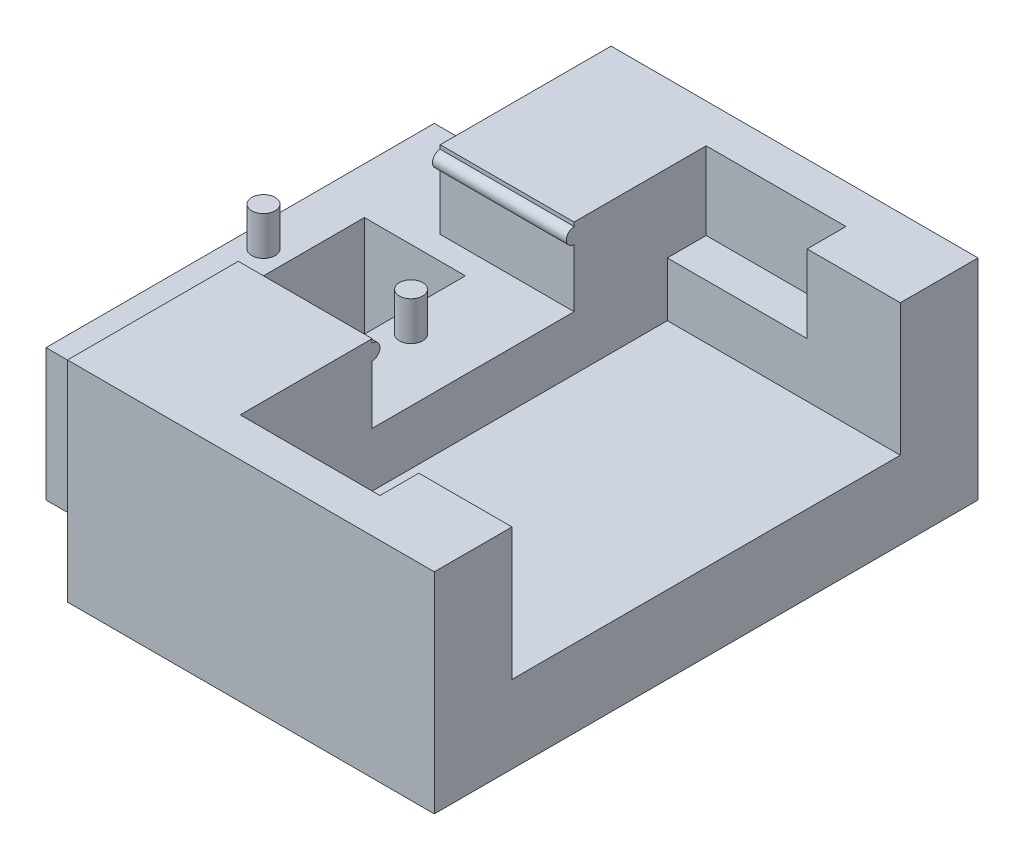
SolidWorks part; units mm, degrees
ref_plane "Front Plane" through (0, 0, 0) normal (0, 0, 1) x (1, 0, 0)
ref_plane "Top Plane" through (0, 0, 0) normal (0, 1, 0) x (1, 0, 0)
ref_plane "Right Plane" through (0, 0, 0) normal (1, 0, 0) x (0, 0, -1)
sketch "Sketch1" plane through (0, 0, 0) normal (0, 1, 0) x (1, 0, 0)
  line L1 (0, 0) -> (15.24, 0)
  line L2 (0, 0) -> (0, 12.7)
  line L3 (0, 12.7) -> (15.24, 12.7)
  line L4 (15.24, 0) -> (15.24, 12.7)
extrude "Main Base" add sketch "Sketch1" along normal blind 2.54
sketch "Sketch2" plane through (0, 2.54, 0) normal (0, 1, 0) x (-1, 0, 0)
  line L0 (0, -6.35) -> (-15.24, -6.35) construction
  line L1 (0, -12.7) -> (0, 0) construction
  line L2 (-15.24, 0) -> (-15.24, -12.7) construction
  circle A0 centre (-0.762, -6.35) radius 0.381
  circle A1 centre (-5.588, -6.35) radius 0.381
extrude "AlignmentPins" add sketch "Sketch2" along normal blind 1.27 from offset 1.778
sketch "Sketch7" plane through (0, 2.54, 0) normal (0, 1, 0) x (1, 0, 0)
  line L0 (0, 0) -> (15.24, 0) construction
  line L1 (0, 12.7) -> (7.62, 12.7)
  line L2 (0, 12.7) -> (0, 0)
  line L3 (0, 0) -> (7.62, 0)
  line L4 (7.62, 12.7) -> (7.62, 0)
extrude "PCBoardEdges" add sketch "Sketch7" along normal blind 1.778
sketch "Sketch12" plane through (0, 4.318, 0) normal (0, 1, 0) x (1, 0, 0)
  line L1 (7.62, 0) -> (3.241, 0)
  line L2 (7.62, 0) -> (7.62, 3.048)
  line L3 (7.62, 3.048) -> (3.241, 3.048)
  line L4 (3.241, 0) -> (3.241, 3.048)
  line L5 (7.62, 12.7) -> (3.241, 12.7)
  line L6 (7.62, 12.7) -> (7.62, 9.652)
  line L7 (7.62, 9.652) -> (3.241, 9.652)
  line L8 (3.241, 12.7) -> (3.241, 9.652)
  dimension "D1" = 6.604
extrude "ConnectorAlign" add sketch "Sketch12" along normal blind 2.54
sketch "Sketch13" plane through (0, 4.318, 0) normal (0, 1, 0) x (1, 0, 0)
  line L2 (4.826, 3.81) -> (1.524, 3.81)
  line L3 (4.826, 3.81) -> (4.826, 8.89)
  line L4 (4.826, 8.89) -> (1.524, 8.89)
  line L5 (1.524, 3.81) -> (1.524, 8.89)
  circle A0 centre (0.762, 6.35) radius 0.381 construction
  point P4 (2.794, 6.35)
  dimension "D1" = 0.762
extrude "LEDHole" cut sketch "Sketch13" against normal through all
sketch "Sketch14" plane through (0, 0, 0) normal (0, 0, 1) x (1, 0, 0)
  line L1 (3.241, 6.858) -> (15.24, 6.858)
  line L2 (3.241, 6.858) -> (3.241, 0)
  line L3 (3.241, 0) -> (15.24, 0)
  line L4 (15.24, 6.858) -> (15.24, 0)
extrude "Shoulder" add sketch "Sketch14" along normal blind 2.54
sketch "Sketch15" plane through (0, 0, -12.7) normal (0, 0, -1) x (-1, 0, 0)
  line L1 (-3.241, 6.858) -> (-15.24, 6.858)
  line L2 (-3.241, 6.858) -> (-3.241, 0)
  line L3 (-3.241, 0) -> (-15.24, 0)
  line L4 (-15.24, 6.858) -> (-15.24, 0)
extrude "Shoulder2" add sketch "Sketch15" along normal blind 2.54
sketch "Sketch17" plane through (7.62, 0, 0) normal (1, 0, 0) x (0, 0, -1)
  line L0 (3.048, 6.858) -> (3.048, 4.318) construction
  line L1 (9.652, 6.858) -> (9.652, 4.318) construction
  circle A0 centre (3.048, 6.477) radius 0.254
  circle A1 centre (9.652, 6.477) radius 0.254
  dimension "D1" = 0.381
extrude "PCB_Clip" add sketch "Sketch17" against normal up to vertex
sketch "Sketch18" plane through (0, 0, 0) normal (0, 0, -1) x (-1, 0, 0)
  line L0 (-15.24, 6.858) -> (-7.62, 6.858) construction
  line L1 (-12.192, 6.858) -> (-7.62, 6.858)
  line L2 (-12.192, 6.858) -> (-12.192, 4.318)
  line L3 (-12.192, 4.318) -> (-7.62, 4.318)
  line L4 (-7.62, 6.858) -> (-7.62, 4.318)
  line L5 (-15.24, 2.54) -> (-15.24, 6.858) construction
  line L6 (-7.62, 6.858) -> (-7.62, 2.54) construction
  dimension "D1" = 3.048
extrude "NunchuckClip" cut sketch "Sketch18" against normal blind 1.27
sketch "Sketch19" plane through (0, 0, -12.7) normal (0, 0, 1) x (1, 0, 0)
  line L0 (7.62, 6.858) -> (15.24, 6.858) construction
  line L1 (7.62, 6.858) -> (12.192, 6.858)
  line L2 (7.62, 6.858) -> (7.62, 4.318)
  line L3 (7.62, 4.318) -> (12.192, 4.318)
  line L4 (12.192, 6.858) -> (12.192, 4.318)
  line L5 (15.24, 6.858) -> (15.24, 2.54) construction
  line L6 (7.62, 6.858) -> (7.62, 2.54) construction
  dimension "D1" = 3.048
extrude "NunchuckClip2" cut sketch "Sketch19" against normal blind 1.27
sketch "Sketch20" plane through (0, 0, 0) normal (0, -1, 0) x (1, 0, 0)
  line L0 (6.017, -0.3687) -> (6.017, -14.8205) construction
  text T0 "E5" font "Gill Sans Ultra Bold Condensed" height 8.382
extrude "Cut-Extrude1" cut sketch "Sketch20" against normal blind 0.508
